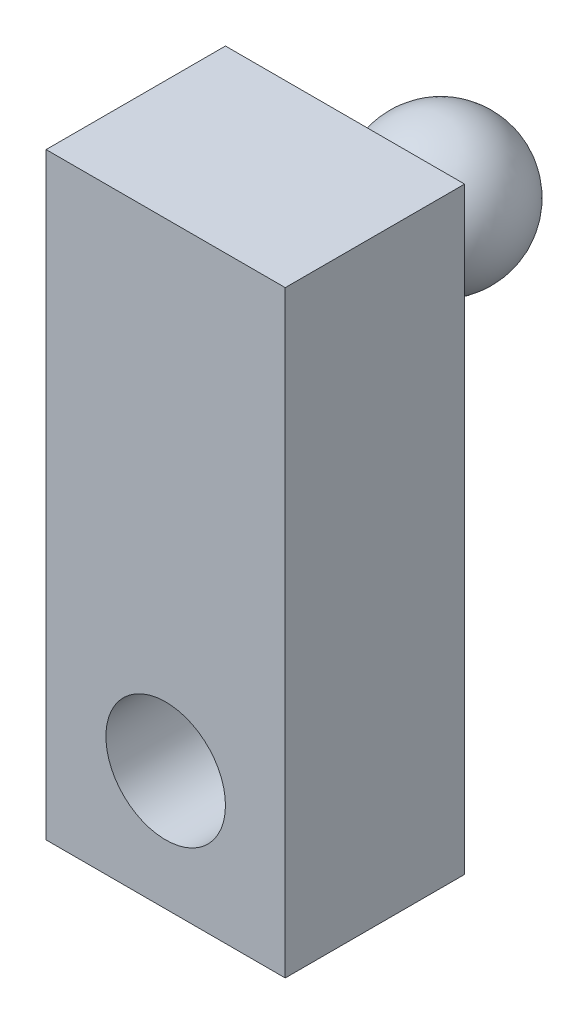
SolidWorks part; units mm, degrees
ref_plane "Front Plane" through (0, 0, 0) normal (0, 0, 1) x (1, 0, 0)
ref_plane "Top Plane" through (0, 0, 0) normal (0, 1, 0) x (1, 0, 0)
ref_plane "Right Plane" through (0, 0, 0) normal (1, 0, 0) x (0, 0, -1)
sketch "Sketch1" plane through (0, 0, 0) normal (0, 0, 1) x (1, 0, 0)
  line L1 (0, 0) -> (25.4, 0)
  line L2 (0, 0) -> (0, 63.5)
  line L3 (0, 63.5) -> (25.4, 63.5)
  line L4 (25.4, 0) -> (25.4, 63.5)
  circle A0 centre (12.7, 12.7) radius 6.35
  dimension "D4" = 12.7
  dimension "D1" = 25.4
  dimension "D2" = 63.5
  dimension "D5" = 12.7
  dimension "D8" = 12.7
extrude "Boss-Extrude1" add sketch "Sketch1" along normal blind 19.05
sketch "Sketch3" plane through (0, 0, 0) normal (0, 0, -1) x (-1, 0, 0)
  line L0 (-25.4, 63.5) -> (0, 63.5) construction
  line L1 (0, 63.5) -> (0, 0) construction
  circle A0 centre (-12.7, 50.8) radius 6.35
  dimension "D1" = 12.7
  dimension "D2" = 12.7
  dimension "D3" = 12.7
extrude "Boss-Extrude3" add sketch "Sketch3" along normal blind 2.54
ref_plane "Plane1" through (0, 0, -10.16) normal (0, 0, -1) x (-1, 0, 0)
sketch "Sketch4" plane through (0, 0, -10.16) normal (0, 0, -1) x (-1, 0, 0)
  line L0 (-12.7, 58.42) -> (-12.7, 43.18)
  arc A0 (-12.7, 58.42) -> (-12.7, 43.18) centre (-12.7, 50.8) ccw
  circle A1 centre (-12.7, 50.8) radius 6.35 construction
  dimension "D1" = 15.24
  dimension "D2" = 0
revolve "Revolve1" add sketch "Sketch4" angle 360 about L0
